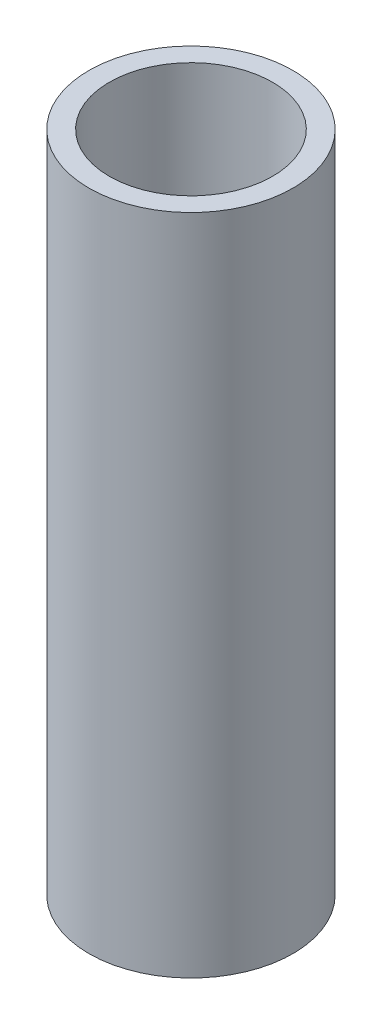
SolidWorks part; units mm, degrees
material "PE High Density"
ref_plane "Front Plane" through (0, 0, 0) normal (0, 0, 1) x (1, 0, 0)
ref_plane "Top Plane" through (0, 0, 0) normal (0, 1, 0) x (1, 0, 0)
ref_plane "Right Plane" through (0, 0, 0) normal (1, 0, 0) x (0, 0, -1)
sketch "Sketch1" plane through (0, 0, 0) normal (0, 1, 0) x (1, 0, 0)
  circle A0 centre (0, 0) radius 25.4
  circle A1 centre (0, 0) radius 31.75
  dimension "D1" = 63.5
  dimension "D2" = 50.8
extrude "Boss-Extrude1" add sketch "Sketch1" along normal blind 206.375
